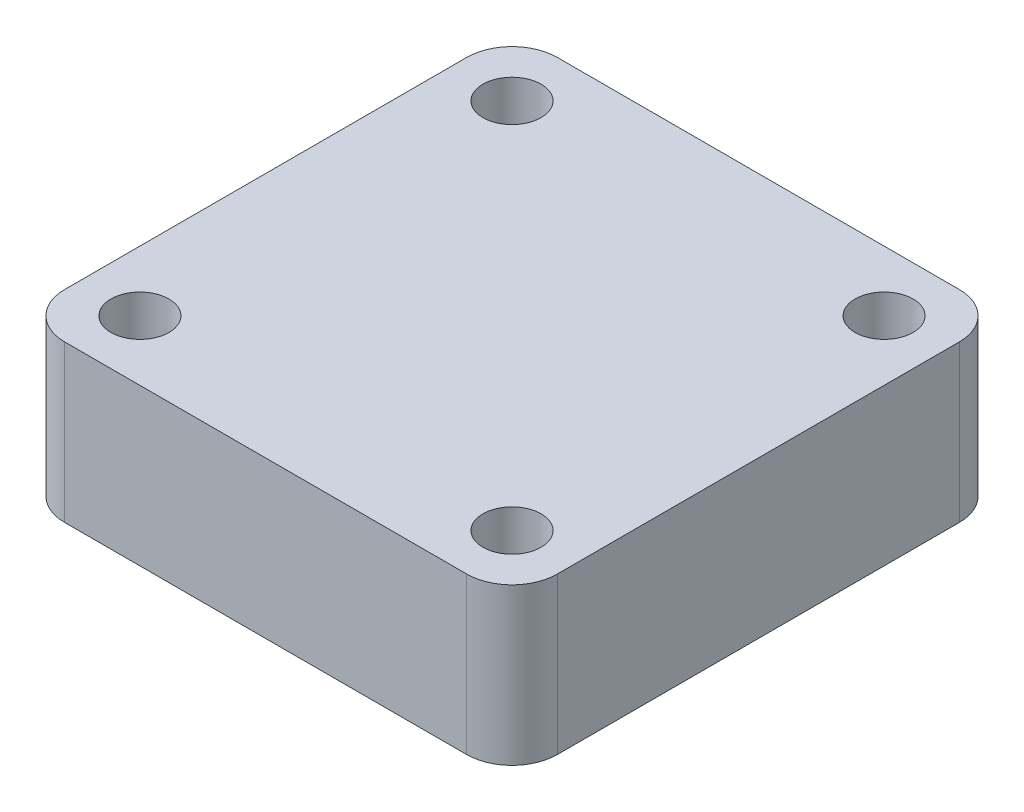
SolidWorks part; units mm, degrees
ref_plane "Front Plane" through (0, 0, 0) normal (0, 0, 1) x (1, 0, 0)
ref_plane "Top Plane" through (0, 0, 0) normal (0, 1, 0) x (1, 0, 0)
ref_plane "Right Plane" through (0, 0, 0) normal (1, 0, 0) x (0, 0, -1)
sketch "Sketch1" plane through (0, 0, 0) normal (0, 1, 0) x (1, 0, 0)
  line L1 (-27.57, -27.57) -> (27.57, -27.57)
  line L2 (-27.57, -27.57) -> (-27.57, 27.57)
  line L3 (-27.57, 27.57) -> (27.57, 27.57)
  line L4 (27.57, -27.57) -> (27.57, 27.57)
  line L5 (-27.57, -27.57) -> (27.57, 27.57) construction
  line L6 (-27.57, 27.57) -> (27.57, -27.57) construction
  point P1 (0, 0)
  dimension "D1" = 55.14
  dimension "D2" = 55.14
extrude "Boss-Extrude1" add sketch "Sketch1" along normal blind 17.5
sketch "Sketch2" plane through (0, 17.5, 0) normal (0, 1, 0) x (1, 0, 0)
  line L0 (27.57, 27.57) -> (-27.57, 27.57) construction
  line L1 (-27.57, 27.57) -> (-27.57, -27.57) construction
  circle A0 centre (-20.82, 20.82) radius 3.25
  dimension "D1" = 6.5
  dimension "D2" = 6.75
  dimension "D3" = 6.75
extrude "Cut-Extrude1" cut sketch "Sketch2" against normal blind 50.8
fillet "Fillet1" radius 5.08 1 edges at (-27.57, 8.75, -27.57)
sketch "Sketch3" plane through (0, 17.5, 0) normal (0, 1, 0) x (1, 0, 0)
  line L0 (27.57, 27.57) -> (-22.49, 27.57) construction
  line L1 (27.57, -27.57) -> (27.57, 27.57) construction
  circle A0 centre (20.82, 20.82) radius 3.25
  dimension "D1" = 6.5
  dimension "D2" = 6.75
  dimension "D3" = 6.75
extrude "Cut-Extrude2" cut sketch "Sketch3" against normal through all both and the other way through all
fillet "Fillet2" radius 5.08 1 edges at (27.57, 8.75, -27.57)
sketch "Sketch10" plane through (0, 17.5, 0) normal (0, 1, 0) x (1, 0, 0)
  line L0 (-27.57, 22.49) -> (-27.57, -27.57) construction
  line L1 (-27.57, -27.57) -> (27.57, -27.57) construction
  circle A0 centre (-20.82, -20.82) radius 3.25
  dimension "D1" = 6.5
  dimension "D2" = 6.75
  dimension "D3" = 6.75
extrude "Cut-Extrude3" cut sketch "Sketch10" against normal through all both and the other way through all
sketch "Sketch11" plane through (0, 17.5, 0) normal (0, 1, 0) x (1, 0, 0)
  line L0 (27.57, -27.57) -> (27.57, 22.49) construction
  line L1 (-27.57, -27.57) -> (27.57, -27.57) construction
  circle A0 centre (20.82, -20.82) radius 3.25
  dimension "D1" = 6.5
  dimension "D2" = 6.75
  dimension "D3" = 6.75
extrude "Cut-Extrude4" cut sketch "Sketch11" against normal through all both
fillet "Fillet3" radius 5.08 2 edges at (-27.57, 8.75, 27.57) (27.57, 8.75, 27.57)
